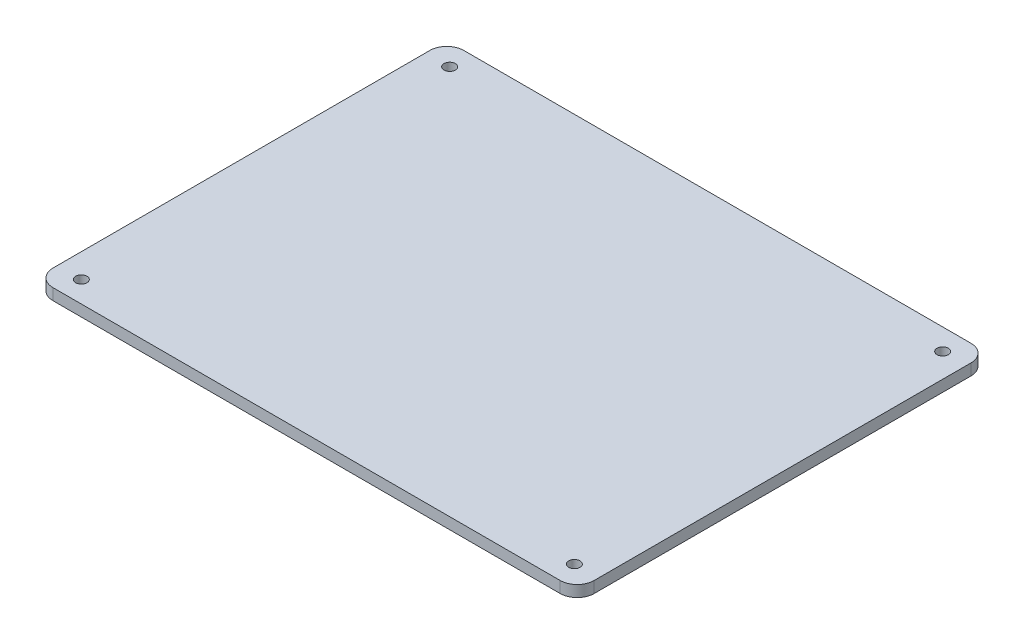
SolidWorks part; units mm, degrees
ref_plane "Спереди" through (0, 0, 0) normal (0, 0, 1) x (1, 0, 0)
ref_plane "Сверху" through (0, 0, 0) normal (0, 1, 0) x (1, 0, 0)
ref_plane "Справа" through (0, 0, 0) normal (1, 0, 0) x (0, 0, -1)
sketch "Эскиз1" plane through (0, 0, 0) normal (0, 1, 0) x (1, 0, 0)
  line L0 (-1000, 0) -> (49000, 0) construction
  line L1 (0, -1000) -> (0, 49000) construction
  line L2 (-1000, -35) -> (49000, -35) construction
  line L3 (-1000, 35) -> (49000, 35) construction
  line L4 (46.5, -1000) -> (46.5, 49000) construction
  line L5 (-46.5, -1000) -> (-46.5, 49000) construction
  line L10 (-47.75, -33.25) -> (-47.75, 33.25)
  line L11 (-44.75, -36.25) -> (44.75, -36.25)
  line L12 (47.75, -33.25) -> (47.75, 33.25)
  line L13 (-44.75, 36.25) -> (44.75, 36.25)
  line L15 (-47.75, -1000) -> (-47.75, 49000) construction
  line L16 (-1000, -36.25) -> (49000, -36.25) construction
  line L17 (-1000, 36.25) -> (49000, 36.25) construction
  line L18 (47.75, -1000) -> (47.75, 49000) construction
  arc A0 (-44.75, 36.25) -> (-47.75, 33.25) centre (-44.75, 33.25) ccw
  arc A1 (47.75, 33.25) -> (44.75, 36.25) centre (44.75, 33.25) ccw
  arc A2 (44.75, -36.25) -> (47.75, -33.25) centre (44.75, -33.25) ccw
  arc A3 (-44.75, -36.25) -> (-47.75, -33.25) centre (-44.75, -33.25) cw
  dimension "D5" = 3
  dimension "D1" = 1.25
  dimension "D2" = 1.25
  dimension "D3" = 1.25
  dimension "D4" = 1.25
extrude "Бобышка-Вытянуть1" add sketch "Эскиз1" along normal blind 2
sketch "Эскиз2" plane through (0, 2, 0) normal (0, 1, 0) x (1, 0, 0)
  line L0 (0, -1000) -> (0, 49000) construction
  line L1 (-1000, 0) -> (49000, 0) construction
  line L2 (43.5, -1000) -> (43.5, 49000) construction
  line L3 (-43.5, -1000) -> (-43.5, 49000) construction
  line L4 (-1000, -32.5) -> (49000, -32.5) construction
  line L5 (-1000, 32.5) -> (49000, 32.5) construction
  circle A0 centre (-43.5, 32.5) radius 2.5
  circle A1 centre (43.5, 32.5) radius 2.5
  circle A2 centre (43.5, -32.5) radius 2.5
  circle A3 centre (-43.5, -32.5) radius 2.5
sketch "Эскиз3" plane through (0, 5, 0) normal (0, 1, 0) x (1, 0, 0)
  circle A0 centre (-43.5, 32.5) radius 1
  circle A1 centre (-43.5, -32.5) radius 1
  circle A2 centre (43.5, -32.5) radius 1
  circle A3 centre (43.5, 32.5) radius 1
extrude "Вырез-Вытянуть1" cut sketch "Эскиз3" against normal blind 13 and the other way blind 3
sketch "Эскиз4" plane through (0, 0, 0) normal (0, -1, 0) x (1, 0, 0)
  line L0 (-1000, 0) -> (49000, 0) construction
  line L1 (0, -1000) -> (0, 49000) construction
  line L2 (17, -1000) -> (17, 49000) construction
  line L3 (-17, -1000) -> (-17, 49000) construction
  line L4 (-1000, -11) -> (49000, -11) construction
  line L5 (-1000, 11) -> (49000, 11) construction
  line L6 (-17, 11) -> (17, 11)
  line L7 (17, 11) -> (17, -11)
  line L8 (17, -11) -> (-17, -11)
  line L9 (-17, -11) -> (-17, 11)
  line L10 (-1000, 11) -> (49000, 11) construction
  line L11 (-1000, -11) -> (49000, -11) construction
extrude "Бобышка-Вытянуть3" add sketch "Эскиз4" along normal blind 3
sketch "Эскиз5" plane through (0, 0, 0) normal (0, -1, 0) x (1, 0, 0)
  line L0 (-15, -1004.1786) -> (-15, 48995.8214) construction
  line L1 (-1016.5797, -11) -> (48983.4203, -11) construction
  line L2 (15, -1005.5591) -> (15, 48994.4409) construction
  line L4 (-1012.8566, 11) -> (48987.1434, 11) construction
  line L8 (-17, -1008.1786) -> (-17, 48991.8214) construction
  line L9 (17, -1005.5591) -> (17, 48994.4409) construction
  line L28 (-15, 11) -> (-15, -11)
  line L29 (-15, -11) -> (-17, -11)
  line L30 (-17, -11) -> (-17, 11)
  line L31 (-17, 11) -> (-15, 11)
  line L32 (15, 11) -> (17, 11)
  line L33 (17, 11) -> (17, -11)
  line L34 (17, -11) -> (17, 11) construction
  line L35 (17, -11) -> (15, -11)
  line L36 (15, -11) -> (15, 11)
extrude "Вырез-Вытянуть3" cut sketch "Эскиз5" along normal blind 1.5
